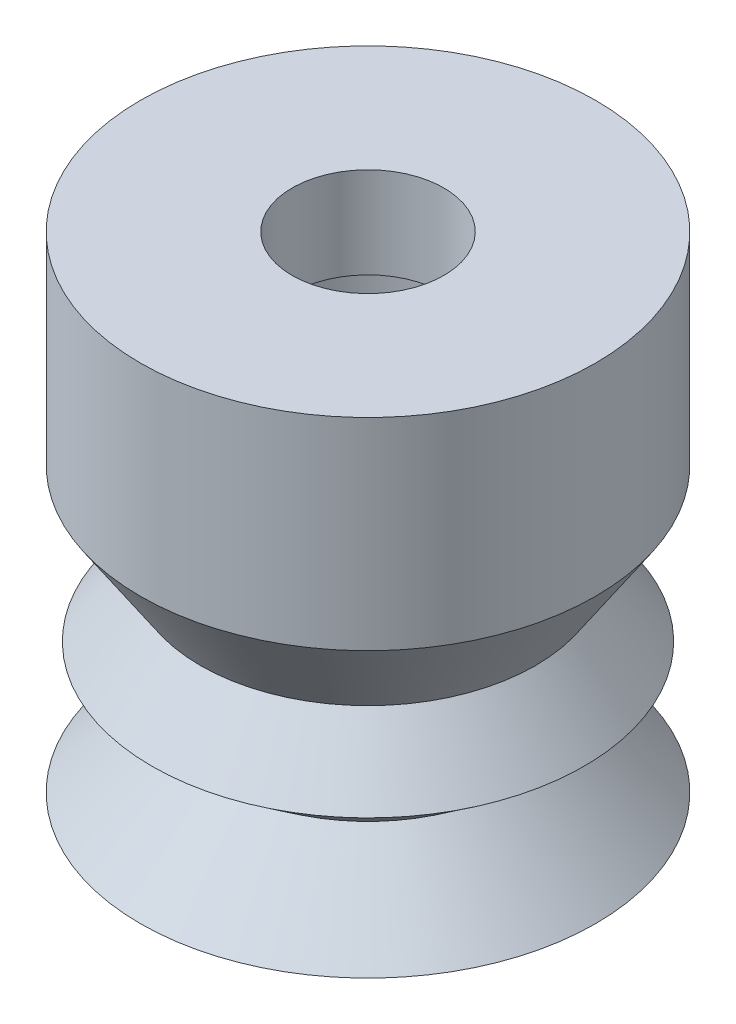
SolidWorks part; units mm, degrees
material "Caoutchouc silicone"
ref_plane "Plan de face" through (0, 0, 0) normal (0, 0, 1) x (1, 0, 0)
ref_plane "Plan de dessus" through (0, 0, 0) normal (0, 1, 0) x (1, 0, 0)
ref_plane "Plan de droite" through (0, 0, 0) normal (1, 0, 0) x (0, 0, -1)
sketch "Esquisse1" plane through (0, 0, 0) normal (0, 0, 1) x (1, 0, 0)
  line L0 (0, 0) -> (0, -16) construction
  line L1 (-2.5, 0) -> (2.5, 0) construction
  line L2 (-3.5, -3) -> (3.5, -3) construction
  line L3 (-2, -5) -> (2, -5) construction
  line L4 (-2.5, 0) -> (-2.5, -3)
  line L5 (-2.5, -3) -> (-3.5, -3)
  line L6 (-3.5, -3) -> (-3.5, -5)
  line L7 (-3.5, -5) -> (-2, -5)
  line L8 (-2, -5) -> (-2, -9.6256)
  line L9 (-7.5, -16) -> (7.5, -16) construction
  line L10 (-3.5, -13.3894) -> (3.5, -13.3894) construction
  line L11 (-2.5, 0) -> (-7.5, 0)
  line L12 (-7.5, 0) -> (-7.5, -6.6563)
  line L13 (-7.5, -6.6563) -> (-5.5188, -9.6256)
  line L14 (-5.5188, -9.6256) -> (-7.1223, -11.6947)
  line L15 (-7.1223, -11.6947) -> (-4.8695, -13.3894)
  line L16 (-4.8695, -13.3894) -> (-7.5, -16)
  line L17 (-7.5, -16) -> (-3.5, -13.3894)
  line L19 (-5.7956, -11.6947) -> (-2, -9.6256)
  line L20 (-3.5, -13.3894) -> (-4.8695, -13.3894) construction
  line L21 (-5.7956, -11.6947) -> (-7.1223, -11.6947) construction
  line L22 (-5.7956, -11.6947) -> (-3.5, -13.3894)
  line L23 (-5.5188, -9.6256) -> (-2, -9.6256) construction
  line L24 (7.5, 0) -> (-7.5, 0) construction
  point P6 (0, 0)
  point P9 (0, -3)
  point P12 (0, -5)
  point P18 (0, -16)
  point P21 (0, -13.3894)
  point P30 (0, 0)
  dimension "D1" = 16
  dimension "D2" = 5
  dimension "D3" = 7
  dimension "D4" = 4
  dimension "D5" = 3
  dimension "D6" = 2
  dimension "D7" = 15
  dimension "D8" = 7
  dimension "D9" = 15
revolve "Révolution1" add sketch "Esquisse1" angle 360 about L0
